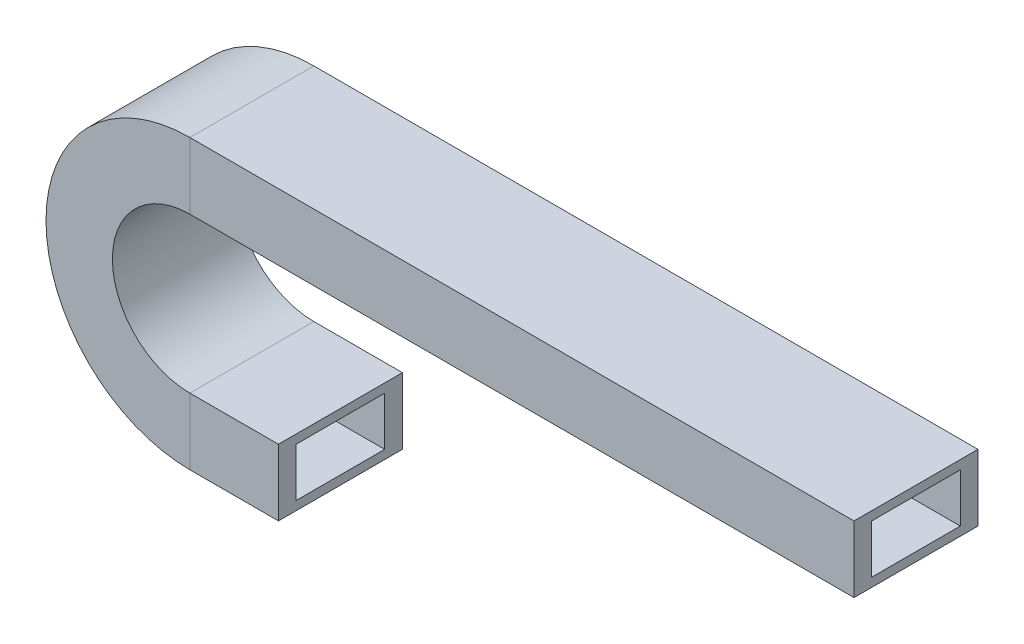
SolidWorks part; units mm, degrees
ref_plane "Front" through (0, 0, 0) normal (0, 0, 1) x (1, 0, 0)
ref_plane "Top" through (0, 0, 0) normal (0, 1, 0) x (1, 0, 0)
ref_plane "Right" through (0, 0, 0) normal (1, 0, 0) x (0, 0, -1)
sketch "Sketch1" plane through (0, 0, 0) normal (0, 0, 1) x (1, 0, 0)
  line L0 (0, 0) -> (-20, 0)
  line L1 (-20, 50) -> (130, 50)
  arc A0 (-20, 0) -> (-20, 50) centre (-20, 25) cw
  dimension "D1" = 25
  dimension "D2" = 20
  dimension "D3" = 150
sketch "Sketch2" plane through (0, 0, 0) normal (1, 0, 0) x (0, 0, -1)
  line L1 (-14, 7.5) -> (14, 7.5)
  line L2 (-14, 7.5) -> (-14, -7.5)
  line L3 (-14, -7.5) -> (14, -7.5)
  line L4 (14, 7.5) -> (14, -7.5)
  line L5 (-14, 7.5) -> (14, -7.5) construction
  line L6 (-14, -7.5) -> (14, 7.5) construction
  line L7 (-10, 5.5) -> (10, 5.5)
  line L8 (-10, 5.5) -> (-10, -5.5)
  line L9 (-10, -5.5) -> (10, -5.5)
  line L10 (10, 5.5) -> (10, -5.5)
  line L11 (-10, 5.5) -> (10, -5.5) construction
  line L12 (-10, -5.5) -> (10, 5.5) construction
  point P0 (0, 0)
  point P5 (0, 0)
  dimension "D1" = 15
  dimension "D2" = 28
  dimension "D3" = 11
  dimension "D4" = 20
sweep "Sweep1" add profiles "Sketch2" path "Sketch1"
